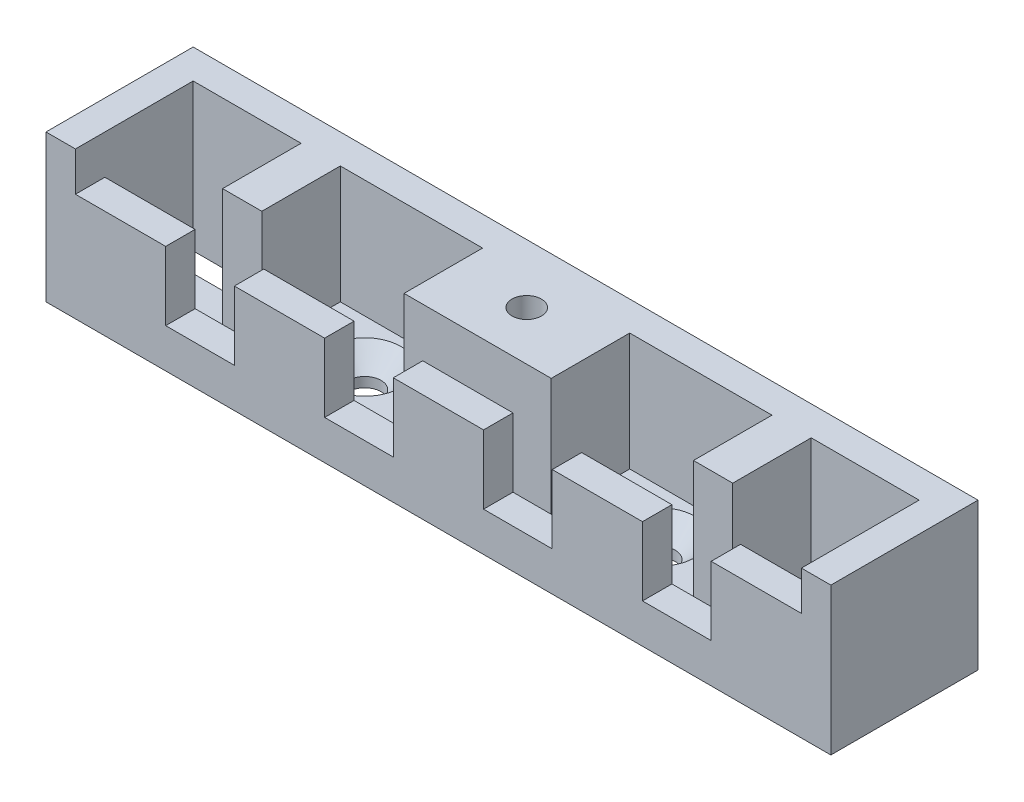
SolidWorks part; units mm, degrees
ref_plane "Ebene vorne" through (0, 0, 0) normal (0, 0, 1) x (1, 0, 0)
ref_plane "Ebene oben" through (0, 0, 0) normal (0, 1, 0) x (1, 0, 0)
ref_plane "Ebene rechts" through (0, 0, 0) normal (1, 0, 0) x (0, 0, -1)
sketch "Sketch1" plane through (0, 0, 0) normal (0, 1, 0) x (1, 0, 0)
  line L1 (-40, -7.5) -> (40, -7.5)
  line L2 (-40, -7.5) -> (-40, 7.5)
  line L3 (-40, 7.5) -> (40, 7.5)
  line L4 (40, -7.5) -> (40, 7.5)
  line L5 (-40, -7.5) -> (40, 7.5) construction
  line L6 (-40, 7.5) -> (40, -7.5) construction
  line L7 (-37, 4.5) -> (-27, 4.5)
  line L8 (-37, 4.5) -> (-37, -0.5)
  line L9 (-37, -0.5) -> (-27, -0.5)
  line L10 (-27, 4.5) -> (-27, -0.5)
  line L11 (27, -0.5) -> (37, -0.5)
  line L12 (27, -0.5) -> (27, 4.5)
  line L13 (27, 4.5) -> (37, 4.5)
  line L14 (37, -0.5) -> (37, 4.5)
  circle A0 centre (-15, 0) radius 1.65
  circle A1 centre (15, 0) radius 1.65
  point P0 (0, 0)
  dimension "D3" = 3.3
  dimension "D4" = 3.3
  dimension "D1" = 15
  dimension "D2" = 80
  dimension "D5" = 15
  dimension "D6" = 15
  dimension "D7" = 5
  dimension "D8" = 10
  dimension "D9" = 10
  dimension "D10" = 5
  dimension "D11" = 3
  dimension "D12" = 3
  dimension "D13" = 3
  dimension "D14" = 3
extrude "Extrude1" add sketch "Sketch1" along normal blind 3
sketch "Sketch2" plane through (0, 3, 0) normal (0, 1, 0) x (1, 0, 0)
  line L0 (40, 7.5) -> (-40, 7.5) construction
  line L1 (-40, -7.5) -> (-37, -7.5)
  line L2 (-40, -7.5) -> (-40, 7.5)
  line L3 (-40, 7.5) -> (-37, 7.5)
  line L4 (-37, -7.5) -> (-37, 7.5)
  line L5 (40, -7.5) -> (40, 7.5) construction
  line L6 (-40, 7.5) -> (40, 7.5)
  line L7 (-40, 7.5) -> (-40, 4.5)
  line L8 (-40, 4.5) -> (40, 4.5)
  line L9 (40, 7.5) -> (40, 4.5)
  line L11 (-40, -7.5) -> (40, -7.5)
  line L12 (-40, -7.5) -> (-40, -4.5)
  line L13 (-40, -4.5) -> (40, -4.5)
  line L14 (40, -7.5) -> (40, -4.5)
  line L15 (40, -7.5) -> (37, -7.5)
  line L16 (40, -7.5) -> (40, 7.5)
  line L17 (40, 7.5) -> (37, 7.5)
  line L18 (37, -7.5) -> (37, 7.5)
  line M8 (40, -7.5) -> (40, 7.5)
  line M9 (40, 7.5) -> (-40, 7.5)
  line M10 (-40, 7.5) -> (-40, -7.5)
  line M11 (-40, -7.5) -> (40, -7.5)
  dimension "D1" = 3
  dimension "D2" = 3
  dimension "D3" = 3
  dimension "D4" = 3
extrude "Extrude2" add sketch "Sketch2" along normal blind 12 contours L8 L4 M10 M9 | L2 L13 L4 L8 | L8 L18 L6 L4 | L13 L4 M10 M11 | L18 L13 L4 M11 | L18 L8 M8 M9 | L18 L13 L8 M8 | L18 L11 L13 M8
sketch "Sketch3" plane through (0, 0, 7.5) normal (0, 0, 1) x (1, 0, 0)
  line L0 (-40, 0) -> (40, 0) construction
  line L1 (-11.6, 11) -> (-4.6, 11)
  line L2 (-11.6, 11) -> (-11.6, 4)
  line L3 (-11.6, 4) -> (-4.6, 4)
  line L4 (-4.6, 11) -> (-4.6, 4)
  line L5 (-40, 15) -> (40, 15) construction
  line L6 (4.6, 4) -> (11.6, 4)
  line L7 (4.6, 4) -> (4.6, 11)
  line L8 (4.6, 11) -> (11.6, 11)
  line L9 (11.6, 4) -> (11.6, 11)
  line L10 (20.8, 4) -> (27.8, 4)
  line L11 (20.8, 4) -> (20.8, 11)
  line L12 (20.8, 11) -> (27.8, 11)
  line L13 (27.8, 4) -> (27.8, 11)
  line L14 (-27.8, 4) -> (-20.8, 4)
  line L15 (-27.8, 4) -> (-27.8, 11)
  line L16 (-27.8, 11) -> (-20.8, 11)
  line L17 (-20.8, 4) -> (-20.8, 11)
  line L18 (-37, 15) -> (37, 15)
  line L19 (-37, 15) -> (-37, 11)
  line L20 (-37, 11) -> (37, 11)
  line L21 (37, 15) -> (37, 11)
  line L22 (-40, 15) -> (-40, 0) construction
  line L23 (40, 15) -> (40, 0) construction
  line M3 (40, 15) -> (-40, 15)
  dimension "D1" = 7
  dimension "D2" = 4
  dimension "D3" = 4.6
  dimension "D4" = 7
  dimension "D5" = 4.6
  dimension "D6" = 7
  dimension "D7" = 7
  dimension "D8" = 9.2
  dimension "D9" = 9.2
  dimension "D10" = 3
  dimension "D11" = 3
extrude "Extrude3" cut sketch "Sketch3" against normal blind 5 contours L21 L19 L20 L16 L1 L8 L12 M3 | L14 L17 L16 L15 | L4 L1 L2 L3 | L6 L9 L8 L7 | L10 L13 L12 L11
chamfer "Chamfer2" distance 2 angle 45 1 edges at (15, 3, 1.65)
chamfer "Chamfer3" distance 2 angle 45 1 edges at (-15, 3, 1.65)
sketch "Sketch4" plane through (0, 3, 0) normal (0, 1, 0) x (1, 0, 0)
  line L0 (-37, 4.5) -> (37, 4.5) construction
  line L1 (-7.5, 4.5) -> (7.5, 4.5)
  line L2 (-7.5, 4.5) -> (-7.5, -3.5)
  line L3 (-7.5, -3.5) -> (7.5, -3.5)
  line L4 (7.5, 4.5) -> (7.5, -3.5)
  line L6 (-27, 4.5) -> (27, 4.5) construction
  line L7 (-26, 4.5) -> (-22, 4.5)
  line L8 (-26, 4.5) -> (-26, -3.5)
  line L9 (-26, -3.5) -> (-22, -3.5)
  line L10 (-22, 4.5) -> (-22, -3.5)
  line L11 (-27, -0.5) -> (-27, 4.5) construction
  line L12 (22, 4.5) -> (26, 4.5)
  line L13 (22, 4.5) -> (22, -3.5)
  line L14 (22, -3.5) -> (26, -3.5)
  line L15 (26, 4.5) -> (26, -3.5)
  dimension "D3" = 8
  dimension "D1" = 15
  dimension "D2" = 7.5
  dimension "D4" = 4
  dimension "D5" = 4
  dimension "D6" = 1
  dimension "D7" = 1
extrude "Extrude4" add sketch "Sketch4" along normal blind 12
sketch "Sketch5" plane through (0, 15, 0) normal (0, 1, 0) x (1, 0, 0)
  line L0 (40, 7.5) -> (-40, 7.5) construction
  circle A0 centre (0, 1.5) radius 1.5
  point P2 (0, 0)
  dimension "D1" = 3
  dimension "D2" = 6
extrude "Extrude5" cut sketch "Sketch5" against normal blind 5
